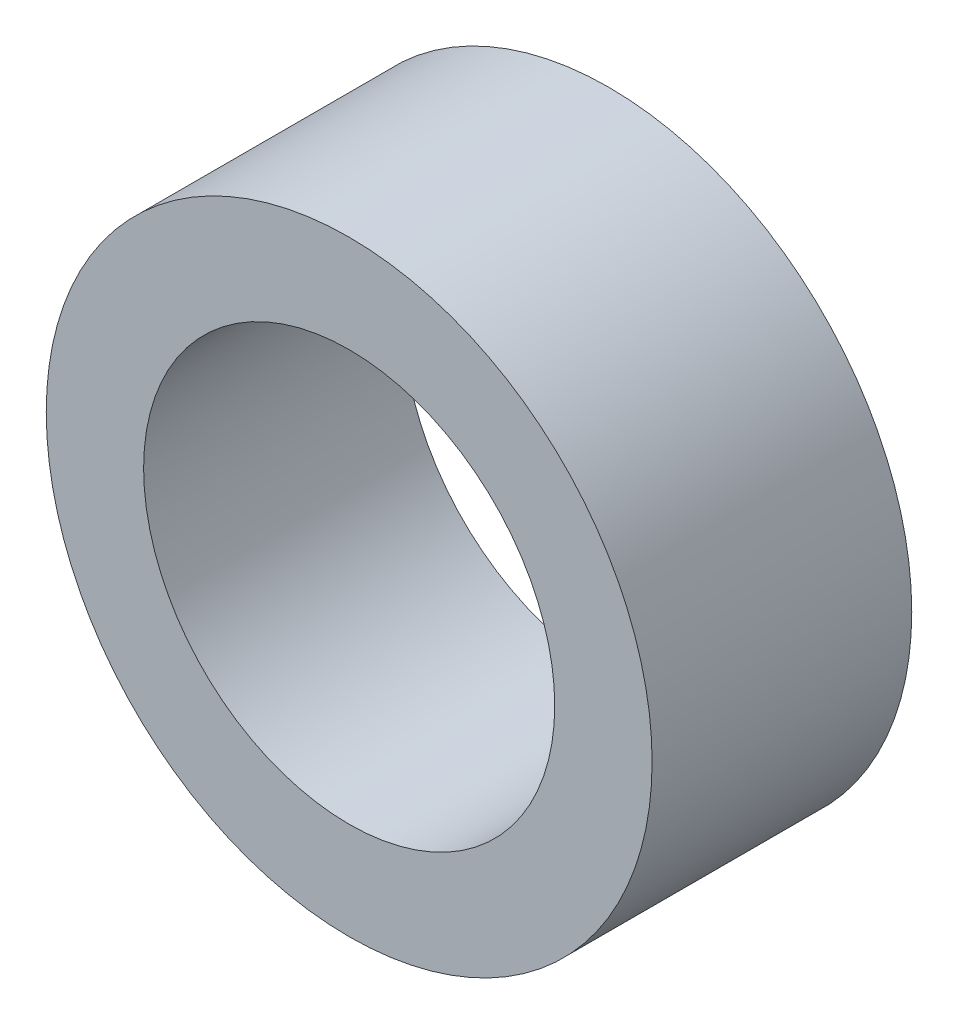
SolidWorks part; units mm, degrees
ref_plane "Front Plane" through (0, 0, 0) normal (0, 0, 1) x (1, 0, 0)
ref_plane "Top Plane" through (0, 0, 0) normal (0, 1, 0) x (1, 0, 0)
ref_plane "Right Plane" through (0, 0, 0) normal (1, 0, 0) x (0, 0, -1)
sketch "Sketch1" plane through (0, 0, 0) normal (0, 0, 1) x (1, 0, 0)
  circle A0 centre (0, 0) radius 2.375
  circle A1 centre (0, 0) radius 3.5
  dimension "D1" = 4.75
  dimension "D2" = 7
extrude "Boss-Extrude1" add sketch "Sketch1" along normal blind 3
